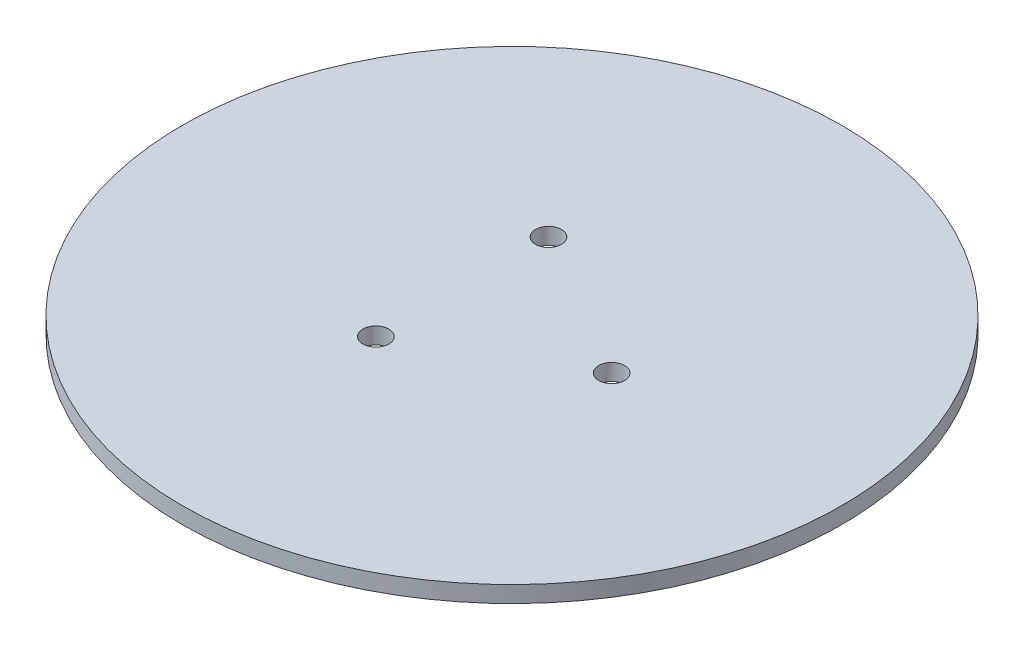
SolidWorks part; units mm, degrees
ref_plane "Front Plane" through (0, 0, 0) normal (0, 0, 1) x (1, 0, 0)
ref_plane "Top Plane" through (0, 0, 0) normal (0, 1, 0) x (1, 0, 0)
ref_plane "Right Plane" through (0, 0, 0) normal (1, 0, 0) x (0, 0, -1)
sketch "Sketch1" plane through (0, 0, 0) normal (0, 1, 0) x (1, 0, 0)
  line L0 (13, 0) -> (25.4, 0) construction
  line L2 (19.2, 0) -> (9.6, 16.6277) construction
  line L3 (9.6, 16.6277) -> (-9.6, 16.6277) construction
  line L4 (-9.6, 16.6277) -> (-19.2, 0) construction
  line L5 (-19.2, 0) -> (-9.6, -16.6277) construction
  line L6 (-9.6, -16.6277) -> (9.6, -16.6277) construction
  line L7 (9.6, -16.6277) -> (19.2, 0) construction
  circle A0 centre (0, 0) radius 63.5
  circle A1 centre (0, 0) radius 25.4 construction
  circle A2 centre (0, 0) radius 13 construction
  circle A3 centre (19.2, 0) radius 2.5
  circle A4 centre (0, 0) radius 16.6277 construction
  circle A5 centre (-9.6, 16.6277) radius 2.5
  circle A6 centre (-9.6, -16.6277) radius 2.5
  dimension "D1" = 127
  dimension "D2" = 50.8
  dimension "D3" = 26
  dimension "D4" = 5
  dimension "D5" = 5
  dimension "D6" = 5
extrude "Boss-Extrude1" add sketch "Sketch1" along normal blind 3.175
